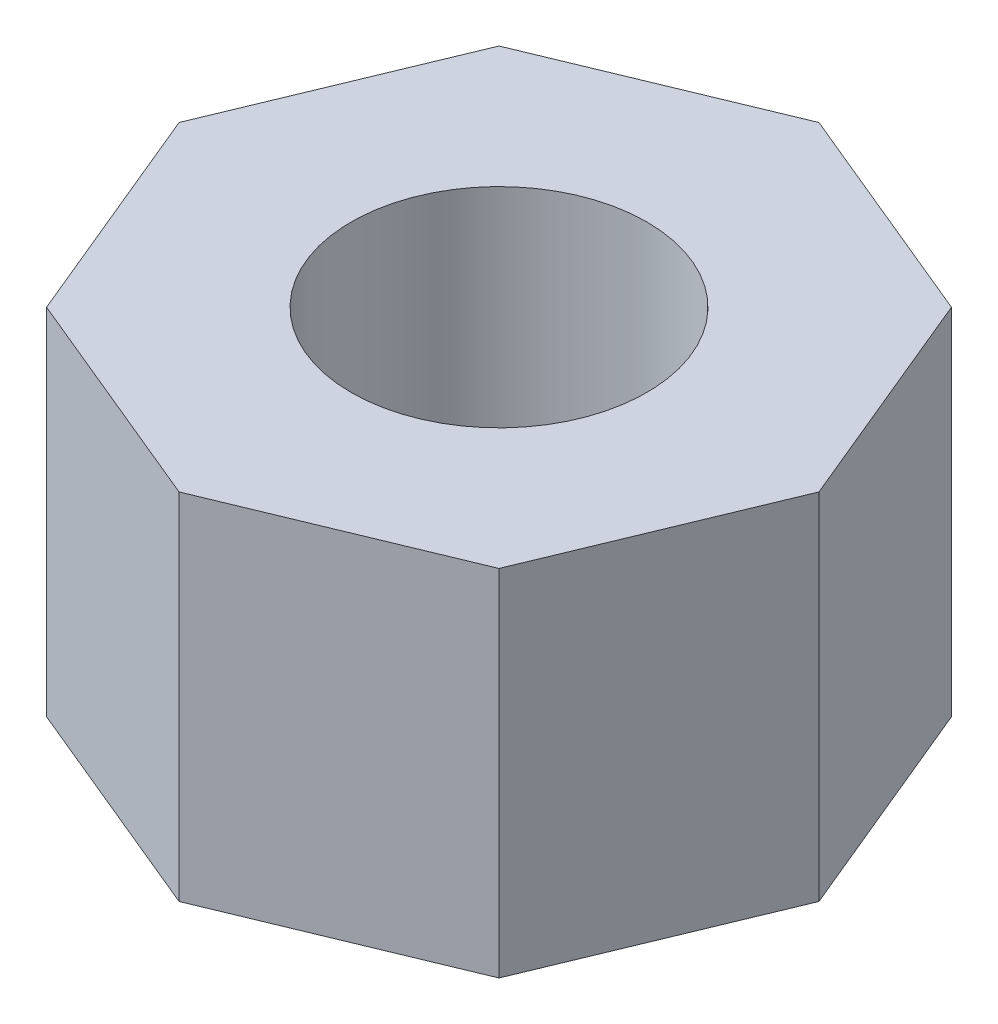
SolidWorks part; units mm, degrees
ref_plane "Front Plane" through (0, 0, 0) normal (0, 0, 1) x (1, 0, 0)
ref_plane "Top Plane" through (0, 0, 0) normal (0, 1, 0) x (1, 0, 0)
ref_plane "Right Plane" through (0, 0, 0) normal (1, 0, 0) x (0, 0, -1)
sketch "Sketch1" plane through (0, 0, 0) normal (0, 1, 0) x (1, 0, 0)
  line L1 (5.412, 0) -> (3.8268, 3.8268)
  line L2 (3.8268, 3.8268) -> (0, 5.412)
  line L3 (0, 5.412) -> (-3.8268, 3.8268)
  line L4 (-3.8268, 3.8268) -> (-5.412, 0)
  line L5 (-5.412, 0) -> (-3.8268, -3.8268)
  line L6 (-3.8268, -3.8268) -> (0, -5.412)
  line L7 (0, -5.412) -> (3.8268, -3.8268)
  line L8 (3.8268, -3.8268) -> (5.412, 0)
  circle A0 centre (0, 0) radius 5 construction
  circle A1 centre (0, 0) radius 2.5
  dimension "D1" = 10
  dimension "D2" = 5
extrude "Boss-Extrude1" add sketch "Sketch1" along normal blind 6 contours L7 L8 L1 L2 L3 L4 L5 L6 A1
cosmetic thread "Cosmetic Thread1"
